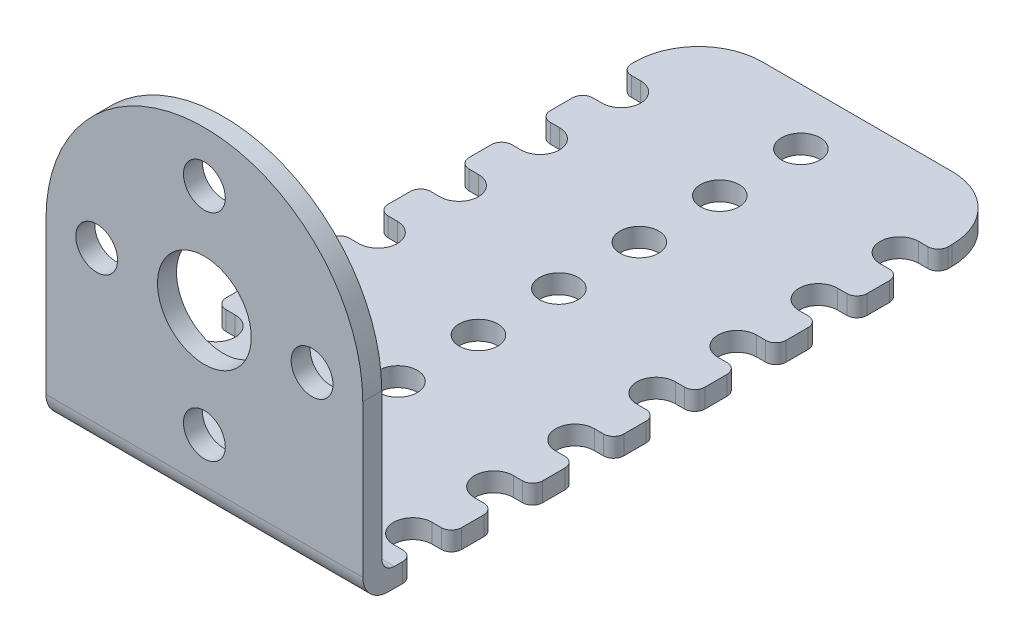
SolidWorks part; units mm, degrees
material "AISI 1010 Aço, barra laminada a quente"
ref_plane "Plano frontal" through (0, 0, 0) normal (0, 0, 1) x (1, 0, 0)
ref_plane "Plano superior" through (0, 0, 0) normal (0, 1, 0) x (1, 0, 0)
ref_plane "Plano direito" through (0, 0, 0) normal (1, 0, 0) x (0, 0, -1)
sketch "Esboço1" plane through (0, 0, 0) normal (0, 1, 0) x (1, 0, 0)
  line L1 (0, 0) -> (25, 0)
  line L2 (0, 0) -> (0, 51.5)
  line L3 (0, 51.5) -> (25, 51.5)
  line L4 (25, 0) -> (25, 51.5)
  dimension "D1" = 51.5
  dimension "D2" = 25
extrude "Ressalto-extrusão1" add sketch "Esboço1" along normal blind 1.5
sketch "Esboço4" plane through (0, 1.5, 0) normal (0, 1, 0) x (1, 0, 0)
  line L0 (25, 0) -> (25, 51.5) construction
  line L1 (0, 0) -> (25, 0)
  line L2 (0, 0) -> (0, 1.5)
  line L3 (0, 1.5) -> (25, 1.5)
  line L4 (25, 0) -> (25, 1.5)
  dimension "D1" = 1.5
extrude "Ressalto-extrusão2" add sketch "Esboço4" along normal blind 25
sketch "Esboço5" plane through (0, 0, 0) normal (0, 0, 1) x (1, 0, 0)
  line L0 (0, 26.5) -> (25, 1.5) construction
  line L1 (25, 26.5) -> (0, 1.5) construction
  line L2 (25, 26.5) -> (25, 0) construction
  line L3 (0, 26.5) -> (25, 26.5) construction
  line L4 (0, 14) -> (25, 14) construction
  line L5 (12.5, 26.5) -> (12.5, 0) construction
  line L6 (0, 0) -> (25, 0) construction
  arc A0 (25, 14) -> (0, 14) centre (12.5, 14) ccw
  circle A1 centre (12.5, 14) radius 3.7
  circle A2 centre (4, 14) radius 1.65
  circle A3 centre (12.5, 22.5) radius 1.65
  circle A4 centre (21, 14) radius 1.65
  circle A5 centre (12.5, 5.5) radius 1.65
  line M2 (25, 0) -> (25, 26.5)
  line M3 (25, 26.5) -> (0, 26.5)
  line M4 (0, 26.5) -> (0, 0)
  dimension "D1" = 7.4
  dimension "D2" = 3.3
  dimension "D3" = 8.5
  dimension "D4" = 4
extrude "Corte-extrusão1" cut sketch "Esboço5" against normal blind 25 contours A2 | A0 M3 M4 | A3 | A1 | A4 | A5 | A0 M2 M3
sketch "Esboço7" plane through (0, 1.5, 0) normal (0, 1, 0) x (1, 0, 0)
  line L0 (1.524, 3.956) -> (0.8, 3.956)
  line L1 (25, 1.5) -> (25, 51.5) construction
  line L2 (25, 51.5) -> (0, 51.5) construction
  line L3 (1.524, 7.004) -> (0.8, 7.004)
  line L5 (23.476, 45.404) -> (24.2, 45.404)
  line L6 (23.476, 42.356) -> (24.2, 42.356)
  line L7 (25, 35.156) -> (25, 39.804)
  line L8 (23.476, 39.004) -> (24.2, 39.004)
  line L9 (25, 41.556) -> (25, 46.204)
  line L10 (23.476, 35.956) -> (24.2, 35.956)
  line L11 (25, 28.756) -> (25, 33.404)
  line L12 (23.476, 32.604) -> (24.2, 32.604)
  line L13 (23.476, 29.556) -> (24.2, 29.556)
  line L14 (25, 22.356) -> (25, 27.004)
  line L15 (23.476, 26.204) -> (24.2, 26.204)
  line L16 (23.476, 23.156) -> (24.2, 23.156)
  line L17 (25, 15.956) -> (25, 20.604)
  line L18 (23.476, 19.804) -> (24.2, 19.804)
  line L19 (23.476, 16.756) -> (24.2, 16.756)
  line L20 (25, 9.556) -> (25, 14.204)
  line L21 (23.476, 13.404) -> (24.2, 13.404)
  line L22 (23.476, 10.356) -> (24.2, 10.356)
  line L23 (25, 3.156) -> (25, 7.804)
  line L24 (23.476, 7.004) -> (24.2, 7.004)
  line L25 (23.476, 3.956) -> (24.2, 3.956)
  line L26 (12.5, 51.5) -> (12.5, 1.5) construction
  line L27 (25, 1.5) -> (0, 1.5) construction
  line L28 (0, 3.156) -> (0, 7.804)
  line L29 (1.524, 10.356) -> (0.8, 10.356)
  line L30 (1.524, 13.404) -> (0.8, 13.404)
  line L31 (0, 9.556) -> (0, 14.204)
  line L32 (1.524, 16.756) -> (0.8, 16.756)
  line L33 (1.524, 19.804) -> (0.8, 19.804)
  line L34 (0, 15.956) -> (0, 20.604)
  line L35 (1.524, 23.156) -> (0.8, 23.156)
  line L36 (1.524, 26.204) -> (0.8, 26.204)
  line L37 (0, 22.356) -> (0, 27.004)
  line L38 (1.524, 29.556) -> (0.8, 29.556)
  line L39 (1.524, 32.604) -> (0.8, 32.604)
  line L40 (0, 28.756) -> (0, 33.404)
  line L41 (1.524, 35.956) -> (0.8, 35.956)
  line L42 (0, 41.556) -> (0, 46.204)
  line L43 (1.524, 39.004) -> (0.8, 39.004)
  line L44 (0, 35.156) -> (0, 39.804)
  line L45 (1.524, 42.356) -> (0.8, 42.356)
  line L46 (1.524, 45.404) -> (0.8, 45.404)
  line L47 (0, 40.68) -> (25, 40.68) construction
  arc A0 (23.476, 45.404) -> (23.476, 42.356) centre (23.476, 43.88) ccw
  arc A1 (25, 46.204) -> (24.2, 45.404) centre (24.2, 46.204) cw
  arc A2 (25, 41.556) -> (24.2, 42.356) centre (24.2, 41.556) ccw
  arc A3 (25, 35.156) -> (24.2, 35.956) centre (24.2, 35.156) ccw
  arc A4 (25, 39.804) -> (24.2, 39.004) centre (24.2, 39.804) cw
  arc A5 (23.476, 39.004) -> (23.476, 35.956) centre (23.476, 37.48) ccw
  arc A6 (25, 28.756) -> (24.2, 29.556) centre (24.2, 28.756) ccw
  arc A7 (25, 33.404) -> (24.2, 32.604) centre (24.2, 33.404) cw
  arc A8 (23.476, 32.604) -> (23.476, 29.556) centre (23.476, 31.08) ccw
  arc A9 (25, 22.356) -> (24.2, 23.156) centre (24.2, 22.356) ccw
  arc A10 (25, 27.004) -> (24.2, 26.204) centre (24.2, 27.004) cw
  arc A11 (23.476, 26.204) -> (23.476, 23.156) centre (23.476, 24.68) ccw
  arc A12 (25, 15.956) -> (24.2, 16.756) centre (24.2, 15.956) ccw
  arc A13 (25, 20.604) -> (24.2, 19.804) centre (24.2, 20.604) cw
  arc A14 (23.476, 19.804) -> (23.476, 16.756) centre (23.476, 18.28) ccw
  arc A15 (25, 9.556) -> (24.2, 10.356) centre (24.2, 9.556) ccw
  arc A16 (25, 14.204) -> (24.2, 13.404) centre (24.2, 14.204) cw
  arc A17 (23.476, 13.404) -> (23.476, 10.356) centre (23.476, 11.88) ccw
  arc A18 (25, 3.156) -> (24.2, 3.956) centre (24.2, 3.156) ccw
  arc A19 (25, 7.804) -> (24.2, 7.004) centre (24.2, 7.804) cw
  arc A20 (23.476, 7.004) -> (23.476, 3.956) centre (23.476, 5.48) ccw
  arc A21 (1.524, 7.004) -> (1.524, 3.956) centre (1.524, 5.48) cw
  arc A22 (0, 7.804) -> (0.8, 7.004) centre (0.8, 7.804) ccw
  arc A23 (0, 3.156) -> (0.8, 3.956) centre (0.8, 3.156) cw
  arc A24 (1.524, 13.404) -> (1.524, 10.356) centre (1.524, 11.88) cw
  arc A25 (0, 14.204) -> (0.8, 13.404) centre (0.8, 14.204) ccw
  arc A26 (0, 9.556) -> (0.8, 10.356) centre (0.8, 9.556) cw
  arc A27 (1.524, 19.804) -> (1.524, 16.756) centre (1.524, 18.28) cw
  arc A28 (0, 20.604) -> (0.8, 19.804) centre (0.8, 20.604) ccw
  arc A29 (0, 15.956) -> (0.8, 16.756) centre (0.8, 15.956) cw
  arc A30 (1.524, 26.204) -> (1.524, 23.156) centre (1.524, 24.68) cw
  arc A31 (0, 27.004) -> (0.8, 26.204) centre (0.8, 27.004) ccw
  arc A32 (0, 22.356) -> (0.8, 23.156) centre (0.8, 22.356) cw
  arc A33 (1.524, 32.604) -> (1.524, 29.556) centre (1.524, 31.08) cw
  arc A34 (0, 33.404) -> (0.8, 32.604) centre (0.8, 33.404) ccw
  arc A35 (0, 28.756) -> (0.8, 29.556) centre (0.8, 28.756) cw
  arc A36 (1.524, 39.004) -> (1.524, 35.956) centre (1.524, 37.48) cw
  arc A37 (0, 39.804) -> (0.8, 39.004) centre (0.8, 39.804) ccw
  arc A38 (0, 35.156) -> (0.8, 35.956) centre (0.8, 35.156) cw
  arc A39 (0, 41.556) -> (0.8, 42.356) centre (0.8, 41.556) cw
  arc A40 (0, 46.204) -> (0.8, 45.404) centre (0.8, 46.204) ccw
  arc A41 (1.524, 45.404) -> (1.524, 42.356) centre (1.524, 43.88) cw
  circle A42 centre (12.5, 40.68) radius 1.524
  circle A43 centre (12.5, 34.33) radius 1.524
  circle A44 centre (12.5, 27.98) radius 1.524
  circle A45 centre (12.5, 21.63) radius 1.524
  circle A46 centre (12.5, 15.28) radius 1.524
  circle A47 centre (12.5, 8.93) radius 1.524
  circle A48 centre (12.5, 47.08) radius 1.524
  point P17 (25, 45.404)
  point P20 (25, 42.356)
  point P136 (0, 42.356)
  point P137 (0, 45.404)
  dimension "D1" = 3.048
  dimension "D3" = 0.8
  dimension "D4" = 0.8
  dimension "D6" = 3.048
  dimension "D2" = 7.62
  dimension "D7" = 6
  dimension "D5" = 7
  dimension "D8" = 2
extrude "Corte-extrusão2" cut sketch "Esboço7" against normal blind 25
fillet "Filete1" radius 5 2 edges at (0, 0.75, -51.5) (25, 0.75, -51.5)
fillet "Filete2" radius 2 1 edges at (12.5, 0, 0)
fillet "Filete3" radius 1 1 edges
